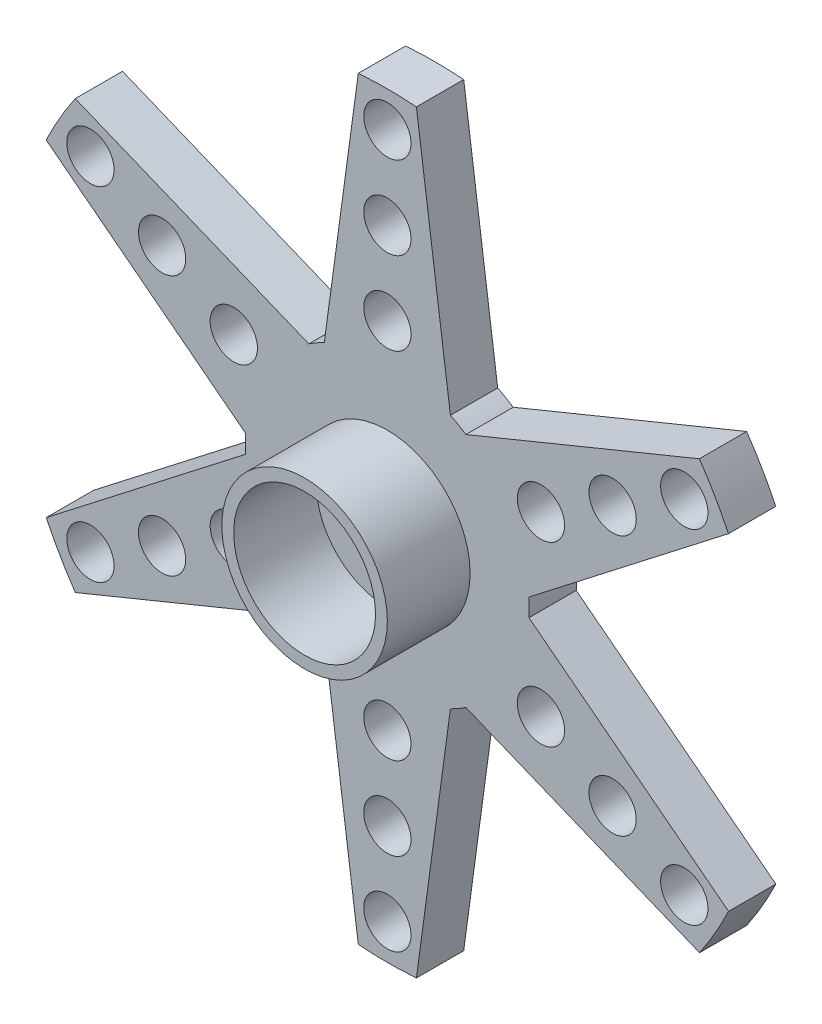
SolidWorks part; units mm, degrees
material "PE High Density"
ref_plane "Front Plane" through (0, 0, 0) normal (0, 0, 1) x (1, 0, 0)
ref_plane "Top Plane" through (0, 0, 0) normal (0, 1, 0) x (1, 0, 0)
ref_plane "Right Plane" through (0, 0, 0) normal (1, 0, 0) x (0, 0, -1)
sketch "Sketch1" plane through (0, 0, 0) normal (0, 0, 1) x (1, 0, 0)
  line L0 (0, 21.0736) -> (0, -16) construction
  line L1 (-16, 0) -> (16, 0) construction
  line L2 (-15.1935, 8.772) -> (15.1935, -8.772) construction
  line L3 (13.8564, 8) -> (-13.8564, -8) construction
  line L4 (-8, 13.8564) -> (8, -13.8564) construction
  line L5 (8, 13.8564) -> (-8, -13.8564) construction
  line L6 (0, 25) -> (-2.75, 4.7631)
  line L7 (-2.75, 4.7631) -> (-21.6506, 12.5)
  line L8 (-21.6506, 12.5) -> (-5.5, 0)
  line L9 (-5.5, 0) -> (-21.6437, -12.512)
  line L10 (-21.6437, -12.512) -> (-2.75, -4.7631)
  line L11 (-2.75, -4.7631) -> (0, -25)
  line L12 (0, -25) -> (2.75, -4.7631)
  line L13 (2.75, -4.7631) -> (21.6506, -12.5)
  line L14 (21.6506, -12.5) -> (5.5, 0)
  line L15 (5.5, 0) -> (21.6437, 12.512)
  line L16 (21.6437, 12.512) -> (2.75, 4.7631)
  line L17 (0, 25) -> (2.75, 4.7631)
  circle A0 centre (0, 0) radius 16
  circle A1 centre (0, 0) radius 5 construction
  circle A2 centre (0, 0) radius 6
  circle A3 centre (0, 0) radius 5.5
  circle A4 centre (0, 0) radius 25
  circle A5 centre (-12.5574, 7.25) radius 1
  circle A6 centre (-9.5263, 5.5) radius 1
  circle A7 centre (-6.4952, 3.75) radius 1
  circle A8 centre (0, 14.5) radius 1
  circle A9 centre (0, 11) radius 1
  circle A10 centre (0, 7.5) radius 1
  circle A11 centre (12.5574, 7.25) radius 1
  circle A12 centre (9.5263, 5.5) radius 1
  circle A13 centre (6.4952, 3.75) radius 1
  circle A14 centre (12.5574, -7.25) radius 1
  circle A15 centre (9.5263, -5.5) radius 1
  circle A16 centre (6.4952, -3.75) radius 1
  circle A17 centre (0, -14.5) radius 1
  circle A18 centre (0, -11) radius 1
  circle A19 centre (0, -7.5) radius 1
  circle A20 centre (-12.5574, -7.25) radius 1
  circle A21 centre (-9.5263, -5.5) radius 1
  circle A22 centre (-6.4952, -3.75) radius 1
  point P69 (0, 0)
  dimension "D1" = 32
  dimension "D2" = 10
  dimension "D3" = 12
  dimension "D4" = 60
  dimension "D8" = 50
  dimension "D9" = 11
  dimension "D10" = 2
  dimension "D11" = 14.5
  dimension "D5" = 60
  dimension "D6" = 30
  dimension "D7" = 30
  dimension "D12" = 3
  dimension "D13" = 6
extrude "Boss-Extrude3" add sketch "Sketch1" along normal blind 2 contours A3 | A3 L9 A2 L10 | A2 L7 A0 L8 A7 A6 A5 | A2 L9 A0 L10 A22 A21 A20 | A2 L11 A0 L12 A19 A18 A17 | A2 L13 A0 L14 A16 A15 A14 | A2 L15 A0 L16 A13 A12 A11 | A2 L17 A0 L6 A10 A9 A8
sketch "Sketch2" plane through (0, 0, 2) normal (0, 0, 1) x (1, 0, 0)
  circle A0 centre (0, 0) radius 1.75
  dimension "D1" = 3.5
extrude "Cut-Extrude2" cut sketch "Sketch2" against normal blind 2
sketch "Sketch3" plane through (0, 0, 2) normal (0, 0, 1) x (1, 0, 0)
  circle A0 centre (0, 0) radius 3
  circle A1 centre (0, 0) radius 3.5
  dimension "D1" = 7
  dimension "D2" = 6
extrude "Boss-Extrude4" add sketch "Sketch3" along normal blind 3.5
